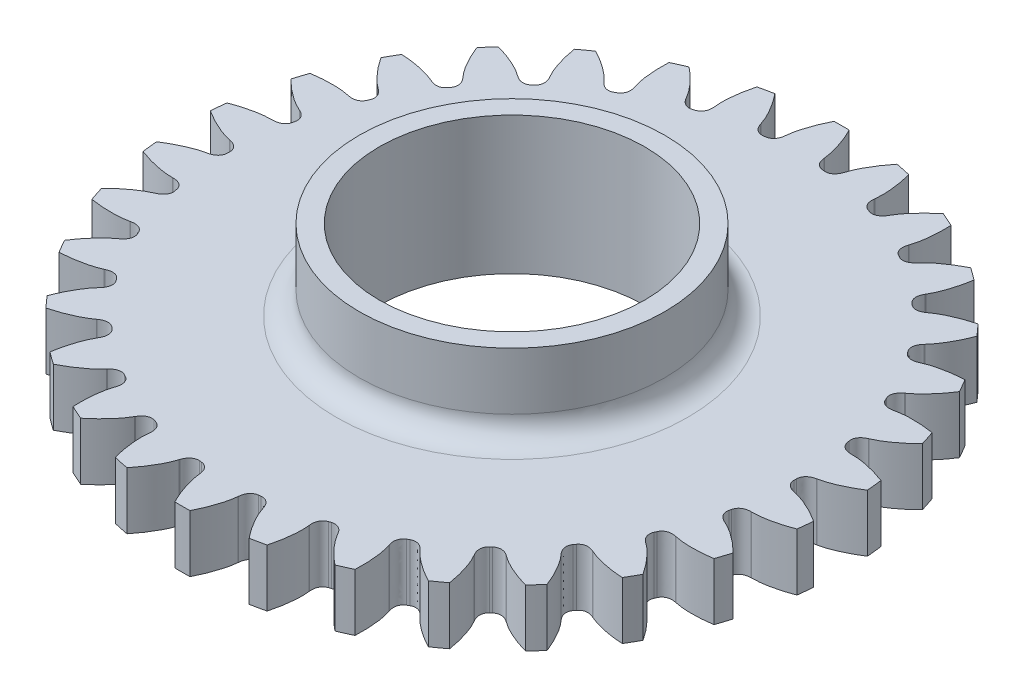
SolidWorks part; units mm, degrees
ref_plane "Front Plane" through (0, 0, 0) normal (0, 0, 1) x (1, 0, 0)
ref_plane "Top Plane" through (0, 0, 0) normal (0, 1, 0) x (1, 0, 0)
ref_plane "Right Plane" through (0, 0, 0) normal (1, 0, 0) x (0, 0, -1)
sketch "Sketch8" plane through (0, 0, 0) normal (0, 1, 0) x (1, 0, 0)
  line L120 (-25.6103, -0.9826) -> (-25.6615, -0.994)
  line L121 (-25.6615, 0.994) -> (-25.6103, 0.9826)
  line L122 (-25.255, 4.3635) -> (-25.3074, 4.363)
  line L123 (-24.894, 6.3076) -> (-24.8464, 6.2858)
  line L124 (-23.7959, 9.519) -> (-23.8472, 9.5294)
  line L125 (-23.0386, 11.3455) -> (-22.9965, 11.3143)
  line L126 (-21.2968, 14.2584) -> (-21.3448, 14.2793)
  line L127 (-20.1763, 15.8876) -> (-20.1416, 15.8483)
  line L128 (-17.8669, 18.3747) -> (-17.9096, 18.4051)
  line L129 (-16.4322, 19.7353) -> (-16.4064, 19.6897)
  line L130 (-13.6562, 21.6879) -> (-13.6916, 21.7265)
  line L131 (-11.9699, 22.7205) -> (-11.9542, 22.6705)
  line L132 (-8.8486, 24.0532) -> (-8.8752, 24.0983)
  line L133 (-6.9845, 24.7127) -> (-6.9795, 24.6605)
  line L134 (-3.6543, 25.3673) -> (-3.6709, 25.417)
  line L135 (-1.6938, 25.6248) -> (-1.6998, 25.5728)
  line L136 (1.6998, 25.5728) -> (1.6938, 25.6248)
  line L137 (3.6709, 25.417) -> (3.6543, 25.3673)
  line L138 (6.9795, 24.6605) -> (6.9845, 24.7127)
  line L139 (8.8752, 24.0983) -> (8.8486, 24.0532)
  line L140 (11.9542, 22.6705) -> (11.9699, 22.7205)
  line L141 (13.6916, 21.7265) -> (13.6562, 21.6879)
  line L142 (16.4064, 19.6897) -> (16.4322, 19.7353)
  line L143 (17.9096, 18.4051) -> (17.8669, 18.3747)
  line L144 (20.1416, 15.8483) -> (20.1763, 15.8876)
  line L145 (21.3448, 14.2793) -> (21.2968, 14.2584)
  line L146 (22.9965, 11.3143) -> (23.0386, 11.3455)
  line L147 (23.8472, 9.5294) -> (23.7959, 9.519)
  line L148 (24.8464, 6.2858) -> (24.894, 6.3076)
  line L149 (25.3074, 4.363) -> (25.255, 4.3635)
  line L150 (25.6103, 0.9826) -> (25.6615, 0.994)
  line L151 (25.6615, -0.994) -> (25.6103, -0.9826)
  line L152 (25.255, -4.3635) -> (25.3074, -4.363)
  line L153 (24.894, -6.3076) -> (24.8464, -6.2858)
  line L154 (23.7959, -9.519) -> (23.8472, -9.5294)
  line L155 (23.0386, -11.3455) -> (22.9965, -11.3143)
  line L156 (21.2968, -14.2584) -> (21.3448, -14.2793)
  line L157 (20.1763, -15.8876) -> (20.1416, -15.8483)
  line L158 (17.8669, -18.3747) -> (17.9096, -18.4051)
  line L159 (16.4322, -19.7353) -> (16.4064, -19.6897)
  line L160 (13.6562, -21.6879) -> (13.6916, -21.7265)
  line L161 (11.9699, -22.7205) -> (11.9542, -22.6705)
  line L162 (8.8486, -24.0532) -> (8.8752, -24.0983)
  line L163 (6.9845, -24.7127) -> (6.9795, -24.6605)
  line L164 (3.6543, -25.3673) -> (3.6709, -25.417)
  line L165 (1.6938, -25.6248) -> (1.6998, -25.5728)
  line L166 (-1.6998, -25.5728) -> (-1.6938, -25.6248)
  line L167 (-3.6709, -25.417) -> (-3.6543, -25.3673)
  line L168 (-6.9795, -24.6605) -> (-6.9845, -24.7127)
  line L169 (-8.8752, -24.0983) -> (-8.8486, -24.0532)
  line L170 (-11.9542, -22.6705) -> (-11.9699, -22.7205)
  line L171 (-13.6916, -21.7265) -> (-13.6562, -21.6879)
  line L172 (-16.4064, -19.6897) -> (-16.4322, -19.7353)
  line L173 (-17.9096, -18.4051) -> (-17.8669, -18.3747)
  line L174 (-20.1416, -15.8483) -> (-20.1763, -15.8876)
  line L175 (-21.3448, -14.2793) -> (-21.2968, -14.2584)
  line L176 (-22.9965, -11.3143) -> (-23.0386, -11.3455)
  line L177 (-23.8472, -9.5294) -> (-23.7959, -9.519)
  line L178 (-24.8464, -6.2858) -> (-24.894, -6.3076)
  line L179 (-25.3074, -4.363) -> (-25.255, -4.3635)
  arc A120 (-28.704, -2.3497) -> (-28.5653, -3.6696) centre (0, 0) ccw
  arc A121 (-24.7498, 0.1062) -> (-24.7498, -0.1062) centre (0, 0) ccw
  arc A122 (-28.5653, 3.6696) -> (-28.704, 2.3497) centre (0, 0) ccw
  arc A123 (-24.1869, 5.2496) -> (-24.231, 5.0419) centre (0, 0) ccw
  arc A124 (-27.1781, 9.5284) -> (-27.5882, 8.2662) centre (0, 0) ccw
  arc A125 (-22.5669, 10.1636) -> (-22.6532, 9.9696) centre (0, 0) ccw
  arc A126 (-24.6031, 14.9709) -> (-25.2667, 13.8215) centre (0, 0) ccw
  arc A127 (-19.9606, 14.6335) -> (-20.0854, 14.4616) centre (0, 0) ccw
  arc A128 (-20.9529, 19.759) -> (-21.8409, 18.7727) centre (0, 0) ccw
  arc A129 (-16.4819, 18.4637) -> (-16.6397, 18.3216) centre (0, 0) ccw
  arc A130 (-16.3869, 23.6836) -> (-17.4606, 22.9034) centre (0, 0) ccw
  arc A131 (-12.2829, 21.487) -> (-12.4668, 21.3808) centre (0, 0) ccw
  arc A132 (-11.1047, 26.573) -> (-12.3171, 26.0332) centre (0, 0) ccw
  arc A133 (-7.5471, 23.5712) -> (-7.7491, 23.5056) centre (0, 0) ccw
  arc A134 (-5.3372, 28.3011) -> (-6.6354, 28.0252) centre (0, 0) ccw
  arc A135 (-2.4814, 24.6253) -> (-2.6927, 24.6031) centre (0, 0) ccw
  arc A136 (0.6636, 28.7924) -> (-0.6636, 28.7924) centre (0, 0) ccw
  arc A137 (2.6927, 24.6031) -> (2.4814, 24.6253) centre (0, 0) ccw
  arc A138 (6.6354, 28.0252) -> (5.3372, 28.3011) centre (0, 0) ccw
  arc A139 (7.7491, 23.5056) -> (7.5471, 23.5712) centre (0, 0) ccw
  arc A140 (12.3171, 26.0332) -> (11.1047, 26.573) centre (0, 0) ccw
  arc A141 (12.4668, 21.3808) -> (12.2829, 21.487) centre (0, 0) ccw
  arc A142 (17.4606, 22.9034) -> (16.3869, 23.6836) centre (0, 0) ccw
  arc A143 (16.6397, 18.3216) -> (16.4819, 18.4637) centre (0, 0) ccw
  arc A144 (21.8409, 18.7727) -> (20.9529, 19.759) centre (0, 0) ccw
  arc A145 (20.0854, 14.4616) -> (19.9606, 14.6335) centre (0, 0) ccw
  arc A146 (25.2667, 13.8215) -> (24.6031, 14.9709) centre (0, 0) ccw
  arc A147 (22.6532, 9.9696) -> (22.5669, 10.1636) centre (0, 0) ccw
  arc A148 (27.5882, 8.2662) -> (27.1781, 9.5284) centre (0, 0) ccw
  arc A149 (24.231, 5.0419) -> (24.1869, 5.2496) centre (0, 0) ccw
  arc A150 (28.704, 2.3497) -> (28.5653, 3.6696) centre (0, 0) ccw
  arc A151 (24.7498, -0.1062) -> (24.7498, 0.1062) centre (0, 0) ccw
  arc A152 (28.5653, -3.6696) -> (28.704, -2.3497) centre (0, 0) ccw
  arc A153 (24.1869, -5.2496) -> (24.231, -5.0419) centre (0, 0) ccw
  arc A154 (27.1781, -9.5284) -> (27.5882, -8.2662) centre (0, 0) ccw
  arc A155 (22.5669, -10.1636) -> (22.6532, -9.9696) centre (0, 0) ccw
  arc A156 (24.6031, -14.9709) -> (25.2667, -13.8215) centre (0, 0) ccw
  arc A157 (19.9606, -14.6335) -> (20.0854, -14.4616) centre (0, 0) ccw
  arc A158 (20.9529, -19.759) -> (21.8409, -18.7727) centre (0, 0) ccw
  arc A159 (16.4819, -18.4637) -> (16.6397, -18.3216) centre (0, 0) ccw
  arc A160 (16.3869, -23.6836) -> (17.4606, -22.9034) centre (0, 0) ccw
  arc A161 (12.2829, -21.487) -> (12.4668, -21.3808) centre (0, 0) ccw
  arc A162 (11.1047, -26.573) -> (12.3171, -26.0332) centre (0, 0) ccw
  arc A163 (7.5471, -23.5712) -> (7.7491, -23.5056) centre (0, 0) ccw
  arc A164 (5.3372, -28.3011) -> (6.6354, -28.0252) centre (0, 0) ccw
  arc A165 (2.4814, -24.6253) -> (2.6927, -24.6031) centre (0, 0) ccw
  arc A166 (-0.6636, -28.7924) -> (0.6636, -28.7924) centre (0, 0) ccw
  arc A167 (-2.6927, -24.6031) -> (-2.4814, -24.6253) centre (0, 0) ccw
  arc A168 (-6.6354, -28.0252) -> (-5.3372, -28.3011) centre (0, 0) ccw
  arc A169 (-7.7491, -23.5056) -> (-7.5471, -23.5712) centre (0, 0) ccw
  arc A170 (-12.3171, -26.0332) -> (-11.1047, -26.573) centre (0, 0) ccw
  arc A171 (-12.4668, -21.3808) -> (-12.2829, -21.487) centre (0, 0) ccw
  arc A172 (-17.4606, -22.9034) -> (-16.3869, -23.6836) centre (0, 0) ccw
  arc A173 (-16.6397, -18.3216) -> (-16.4819, -18.4637) centre (0, 0) ccw
  arc A174 (-21.8409, -18.7727) -> (-20.9529, -19.759) centre (0, 0) ccw
  arc A175 (-20.0854, -14.4616) -> (-19.9606, -14.6335) centre (0, 0) ccw
  arc A176 (-25.2667, -13.8215) -> (-24.6031, -14.9709) centre (0, 0) ccw
  arc A177 (-22.6532, -9.9696) -> (-22.5669, -10.1636) centre (0, 0) ccw
  arc A178 (-27.5882, -8.2662) -> (-27.1781, -9.5284) centre (0, 0) ccw
  arc A179 (-24.231, -5.0419) -> (-24.1869, -5.2496) centre (0, 0) ccw
  spline S240 degree 3 poles (-25.6615, -0.994) (-25.8209, -1.0255) (-26.0845, -1.093) (-26.4652, -1.2166) (-26.8252, -1.3524) (-27.2303, -1.5274) (-27.6774, -1.7459) (-28.1632, -2.0124) (-28.5074, -2.2228) (-28.6912, -2.3414) (-28.704, -2.3497) knots 0 0 0 0 0.103847 0.173799 0.255771 0.349761 0.455771 0.573799 0.703847 0.713589 0.713589 0.713589 0.713589
  spline S241 degree 3 poles (-24.7498, -0.1062) (-24.7485, -0.2459) (-24.8034, -0.4407) (-24.9485, -0.6376) (-25.0551, -0.7378) (-25.1596, -0.8112) (-25.2608, -0.8666) (-25.3601, -0.9098) (-25.4756, -0.9499) (-25.5594, -0.9724) (-25.6103, -0.9826) knots 0 0 0 0 0.312247 0.438755 0.546198 0.639977 0.72507 0.805244 0.883176 1 1 1 1
  spline S242 degree 3 poles (-25.6103, 0.9826) (-25.5594, 0.9724) (-25.4756, 0.9499) (-25.3601, 0.9098) (-25.2608, 0.8666) (-25.1596, 0.8112) (-25.0551, 0.7378) (-24.9485, 0.6376) (-24.8034, 0.4407) (-24.7485, 0.2459) (-24.7498, 0.1062) knots 0 0 0 0 0.116824 0.194756 0.27493 0.360023 0.453802 0.561245 0.687753 1 1 1 1
  spline S243 degree 3 poles (-28.704, 2.3497) (-28.6912, 2.3414) (-28.5074, 2.2228) (-28.1632, 2.0124) (-27.6774, 1.7459) (-27.2303, 1.5274) (-26.8252, 1.3524) (-26.4652, 1.2166) (-26.0845, 1.093) (-25.8209, 1.0255) (-25.6615, 0.994) knots 0.286411 0.286411 0.286411 0.286411 0.296153 0.426201 0.544229 0.650239 0.744229 0.826201 0.896153 1 1 1 1
  spline S244 degree 3 poles (-25.3074, 4.363) (-25.4698, 4.3653) (-25.7417, 4.3541) (-26.1398, 4.3124) (-26.5202, 4.2544) (-26.9528, 4.1675) (-27.4356, 4.0467) (-27.9662, 3.887) (-28.3466, 3.7528) (-28.551, 3.675) (-28.5653, 3.6696) knots 0 0 0 0 0.103847 0.173799 0.255771 0.349761 0.455771 0.573799 0.703847 0.713589 0.713589 0.713589 0.713589
  spline S245 degree 3 poles (-24.231, 5.0419) (-24.2588, 4.905) (-24.3531, 4.7259) (-24.5359, 4.5635) (-24.661, 4.4876) (-24.7784, 4.4375) (-24.889, 4.4044) (-24.9951, 4.3828) (-25.1164, 4.3675) (-25.203, 4.363) (-25.255, 4.3635) knots 0 0 0 0 0.312247 0.438755 0.546198 0.639977 0.72507 0.805244 0.883176 1 1 1 1
  spline S246 degree 3 poles (-24.8464, 6.2858) (-24.7987, 6.2652) (-24.7214, 6.2258) (-24.6168, 6.1626) (-24.5286, 6.0997) (-24.4411, 6.0245) (-24.3542, 5.931) (-24.2708, 5.8107) (-24.1698, 5.588) (-24.1566, 5.386) (-24.1869, 5.2496) knots 0 0 0 0 0.116824 0.194756 0.27493 0.360023 0.453802 0.561245 0.687753 1 1 1 1
  spline S247 degree 3 poles (-27.5882, 8.2662) (-27.5774, 8.2554) (-27.4223, 8.1013) (-27.1294, 7.8239) (-26.7096, 7.4622) (-26.3177, 7.1555) (-25.9578, 6.9002) (-25.6339, 6.6924) (-25.2872, 6.4924) (-25.0434, 6.3716) (-24.894, 6.3076) knots 0.286411 0.286411 0.286411 0.286411 0.296153 0.426201 0.544229 0.650239 0.744229 0.826201 0.896153 1 1 1 1
  spline S248 degree 3 poles (-23.8472, 9.5294) (-24.0057, 9.5654) (-24.274, 9.611) (-24.672, 9.6529) (-25.0561, 9.6753) (-25.4974, 9.6802) (-25.9947, 9.6624) (-26.5469, 9.6166) (-26.9469, 9.5644) (-27.163, 9.5308) (-27.1781, 9.5284) knots 0 0 0 0 0.103847 0.173799 0.255771 0.349761 0.455771 0.573799 0.703847 0.713589 0.713589 0.713589 0.713589
  spline S249 degree 3 poles (-22.6532, 9.9696) (-22.7089, 9.8415) (-22.8383, 9.6859) (-23.0509, 9.565) (-23.1891, 9.5168) (-23.3144, 9.4922) (-23.4294, 9.4828) (-23.5376, 9.4838) (-23.6595, 9.4941) (-23.7452, 9.5076) (-23.7959, 9.519) knots 0 0 0 0 0.312247 0.438755 0.546198 0.639977 0.72507 0.805244 0.883176 1 1 1 1
  spline S250 degree 3 poles (-22.9965, 11.3143) (-22.9542, 11.2843) (-22.8868, 11.2297) (-22.7976, 11.146) (-22.7244, 11.0662) (-22.6545, 10.9744) (-22.5889, 10.8649) (-22.5323, 10.7299) (-22.4798, 10.4911) (-22.5089, 10.2907) (-22.5669, 10.1636) knots 0 0 0 0 0.116824 0.194756 0.27493 0.360023 0.453802 0.561245 0.687753 1 1 1 1
  spline S251 degree 3 poles (-25.2667, 13.8215) (-25.2584, 13.8087) (-25.1387, 13.6257) (-24.9099, 13.2934) (-24.5744, 12.8524) (-24.2549, 12.4709) (-23.956, 12.1463) (-23.6823, 11.8758) (-23.3848, 11.6081) (-23.1714, 11.4392) (-23.0386, 11.3455) knots 0.286411 0.286411 0.286411 0.286411 0.296153 0.426201 0.544229 0.650239 0.744229 0.826201 0.896153 1 1 1 1
  spline S252 degree 3 poles (-21.3448, 14.2793) (-21.4923, 14.3475) (-21.7453, 14.4478) (-22.1259, 14.5716) (-22.497, 14.6733) (-22.9275, 14.7699) (-23.4177, 14.8559) (-23.9674, 14.9259) (-24.3695, 14.9579) (-24.5879, 14.9701) (-24.6031, 14.9709) knots 0 0 0 0 0.103847 0.173799 0.255771 0.349761 0.455771 0.573799 0.703847 0.713589 0.713589 0.713589 0.713589
  spline S253 degree 3 poles (-20.0854, 14.4616) (-20.1665, 14.3479) (-20.3254, 14.2226) (-20.5585, 14.1486) (-20.7037, 14.1301) (-20.8314, 14.1321) (-20.9458, 14.1469) (-21.0515, 14.1703) (-21.1686, 14.2057) (-21.2495, 14.2368) (-21.2968, 14.2584) knots 0 0 0 0 0.312247 0.438755 0.546198 0.639977 0.72507 0.805244 0.883176 1 1 1 1
  spline S254 degree 3 poles (-20.1416, 15.8483) (-20.1064, 15.8101) (-20.0519, 15.7427) (-19.982, 15.6423) (-19.9271, 15.549) (-19.8777, 15.4447) (-19.8364, 15.324) (-19.809, 15.1802) (-19.8074, 14.9356) (-19.8775, 14.7457) (-19.9606, 14.6335) knots 0 0 0 0 0.116824 0.194756 0.27493 0.360023 0.453802 0.561245 0.687753 1 1 1 1
  spline S255 degree 3 poles (-21.8409, 18.7727) (-21.8354, 18.7585) (-21.7564, 18.5546) (-21.6017, 18.182) (-21.3653, 17.6809) (-21.132, 17.2412) (-20.9071, 16.8616) (-20.6957, 16.5401) (-20.4603, 16.2164) (-20.2867, 16.0068) (-20.1763, 15.8876) knots 0.286411 0.286411 0.286411 0.286411 0.296153 0.426201 0.544229 0.650239 0.744229 0.826201 0.896153 1 1 1 1
  spline S256 degree 3 poles (-17.9096, 18.4051) (-18.0396, 18.5024) (-18.2662, 18.6532) (-18.6128, 18.8534) (-18.9546, 19.0301) (-19.3557, 19.214) (-19.8173, 19.4001) (-20.3404, 19.5828) (-20.7271, 19.6978) (-20.9381, 19.755) (-20.9529, 19.759) knots 0 0 0 0 0.103847 0.173799 0.255771 0.349761 0.455771 0.573799 0.703847 0.713589 0.713589 0.713589 0.713589
  spline S257 degree 3 poles (-16.6397, 18.3216) (-16.7427, 18.2272) (-16.9243, 18.1377) (-17.1676, 18.1138) (-17.3135, 18.1259) (-17.4379, 18.1544) (-17.5468, 18.1926) (-17.6453, 18.2375) (-17.7525, 18.2965) (-17.8252, 18.3437) (-17.8669, 18.3747) knots 0 0 0 0 0.312247 0.438755 0.546198 0.639977 0.72507 0.805244 0.883176 1 1 1 1
  spline S258 degree 3 poles (-16.4064, 19.6897) (-16.3799, 19.645) (-16.3406, 19.5677) (-16.2931, 19.455) (-16.2588, 19.3523) (-16.2322, 19.24) (-16.2169, 19.1133) (-16.22, 18.967) (-16.2692, 18.7274) (-16.3773, 18.5563) (-16.4819, 18.4637) knots 0 0 0 0 0.116824 0.194756 0.27493 0.360023 0.453802 0.561245 0.687753 1 1 1 1
  spline S259 degree 3 poles (-17.4606, 22.9034) (-17.4582, 22.8884) (-17.4233, 22.6725) (-17.3494, 22.2759) (-17.2223, 21.7366) (-17.0856, 21.2581) (-16.9445, 20.84) (-16.8046, 20.4815) (-16.6416, 20.1159) (-16.5154, 19.8749) (-16.4322, 19.7353) knots 0.286411 0.286411 0.286411 0.286411 0.296153 0.426201 0.544229 0.650239 0.744229 0.826201 0.896153 1 1 1 1
  spline S260 degree 3 poles (-13.6916, 21.7265) (-13.7986, 21.8488) (-13.9888, 22.0433) (-14.2862, 22.3112) (-14.5838, 22.5551) (-14.9379, 22.8184) (-15.3507, 23.0964) (-15.8244, 23.3839) (-16.1787, 23.5767) (-16.3733, 23.6766) (-16.3869, 23.6836) knots 0 0 0 0 0.103847 0.173799 0.255771 0.349761 0.455771 0.573799 0.703847 0.713589 0.713589 0.713589 0.713589
  spline S261 degree 3 poles (-12.4668, 21.3808) (-12.5872, 21.3099) (-12.7834, 21.2601) (-13.0264, 21.2873) (-13.1665, 21.3295) (-13.2823, 21.3832) (-13.3809, 21.4432) (-13.4679, 21.5076) (-13.5605, 21.5876) (-13.6218, 21.6489) (-13.6562, 21.6879) knots 0 0 0 0 0.312247 0.438755 0.546198 0.639977 0.72507 0.805244 0.883176 1 1 1 1
  spline S262 degree 3 poles (-11.9542, 22.6705) (-11.9376, 22.6213) (-11.9152, 22.5375) (-11.8922, 22.4174) (-11.8799, 22.3098) (-11.8773, 22.1944) (-11.8886, 22.0673) (-11.9221, 21.9249) (-12.0201, 21.7008) (-12.1613, 21.5558) (-12.2829, 21.487) knots 0 0 0 0 0.116824 0.194756 0.27493 0.360023 0.453802 0.561245 0.687753 1 1 1 1
  spline S263 degree 3 poles (-12.3171, 26.0332) (-12.3179, 26.018) (-12.3287, 25.7996) (-12.3388, 25.3963) (-12.3267, 24.8423) (-12.2924, 24.3458) (-12.2414, 23.9075) (-12.179, 23.5278) (-12.0956, 23.1364) (-12.0223, 22.8743) (-11.9699, 22.7205) knots 0.286411 0.286411 0.286411 0.286411 0.296153 0.426201 0.544229 0.650239 0.744229 0.826201 0.896153 1 1 1 1
  spline S264 degree 3 poles (-8.8752, 24.0983) (-8.9544, 24.2402) (-9.1001, 24.4701) (-9.3352, 24.7939) (-9.5757, 25.0944) (-9.8672, 25.4256) (-10.2133, 25.7833) (-10.6168, 26.1629) (-10.9233, 26.4253) (-11.0928, 26.5634) (-11.1047, 26.573) knots 0 0 0 0 0.103847 0.173799 0.255771 0.349761 0.455771 0.573799 0.703847 0.713589 0.713589 0.713589 0.713589
  spline S265 degree 3 poles (-7.7491, 23.5056) (-7.8815, 23.4613) (-8.0838, 23.4533) (-8.3159, 23.5304) (-8.4442, 23.6009) (-8.5463, 23.6775) (-8.6302, 23.7567) (-8.7019, 23.8377) (-8.7758, 23.9352) (-8.8231, 24.0079) (-8.8486, 24.0532) knots 0 0 0 0 0.312247 0.438755 0.546198 0.639977 0.72507 0.805244 0.883176 1 1 1 1
  spline S266 degree 3 poles (-6.9795, 24.6605) (-6.9735, 24.6089) (-6.969, 24.5223) (-6.9715, 24.4) (-6.9819, 24.2922) (-7.0032, 24.1789) (-7.0408, 24.0569) (-7.1032, 23.9245) (-7.2456, 23.7257) (-7.4139, 23.6132) (-7.5471, 23.5712) knots 0 0 0 0 0.116824 0.194756 0.27493 0.360023 0.453802 0.561245 0.687753 1 1 1 1
  spline S267 degree 3 poles (-6.6354, 28.0252) (-6.6393, 28.0105) (-6.6952, 27.7991) (-6.789, 27.4067) (-6.8923, 26.8623) (-6.962, 26.3695) (-7.0032, 25.9302) (-7.0211, 25.5458) (-7.021, 25.1456) (-7.0038, 24.874) (-6.9845, 24.7127) knots 0.286411 0.286411 0.286411 0.286411 0.296153 0.426201 0.544229 0.650239 0.744229 0.826201 0.896153 1 1 1 1
  spline S268 degree 3 poles (-3.6709, 25.417) (-3.7189, 25.5722) (-3.8136, 25.8273) (-3.9763, 26.193) (-4.149, 26.5369) (-4.3653, 26.9215) (-4.6294, 27.3433) (-4.9452, 27.7986) (-5.1905, 28.1189) (-5.3276, 28.2893) (-5.3372, 28.3011) knots 0 0 0 0 0.103847 0.173799 0.255771 0.349761 0.455771 0.573799 0.703847 0.713589 0.713589 0.713589 0.713589
  spline S269 degree 3 poles (-2.6927, 24.6031) (-2.8314, 24.5873) (-3.031, 24.6215) (-3.2419, 24.7452) (-3.3528, 24.8408) (-3.4367, 24.937) (-3.5023, 25.0318) (-3.5556, 25.1261) (-3.6076, 25.2368) (-3.6388, 25.3177) (-3.6543, 25.3673) knots 0 0 0 0 0.312247 0.438755 0.546198 0.639977 0.72507 0.805244 0.883176 1 1 1 1
  spline S270 degree 3 poles (-1.6998, 25.5728) (-1.7046, 25.521) (-1.7182, 25.4354) (-1.7461, 25.3163) (-1.7786, 25.213) (-1.8231, 25.1065) (-1.8852, 24.995) (-1.9738, 24.8785) (-2.1544, 24.7136) (-2.3424, 24.6387) (-2.4814, 24.6253) knots 0 0 0 0 0.116824 0.194756 0.27493 0.360023 0.453802 0.561245 0.687753 1 1 1 1
  spline S271 degree 3 poles (-0.6636, 28.7924) (-0.6705, 28.7788) (-0.7692, 28.5836) (-0.9425, 28.2193) (-1.1567, 27.7083) (-1.3273, 27.2408) (-1.459, 26.8196) (-1.5564, 26.4474) (-1.6395, 26.0559) (-1.6791, 25.7866) (-1.6938, 25.6248) knots 0.286411 0.286411 0.286411 0.286411 0.296153 0.426201 0.544229 0.650239 0.744229 0.826201 0.896153 1 1 1 1
  spline S272 degree 3 poles (1.6938, 25.6248) (1.6791, 25.7866) (1.6395, 26.0559) (1.5564, 26.4474) (1.459, 26.8196) (1.3273, 27.2408) (1.1567, 27.7083) (0.9425, 28.2193) (0.7692, 28.5836) (0.6705, 28.7788) (0.6636, 28.7924) knots 0 0 0 0 0.103847 0.173799 0.255771 0.349761 0.455771 0.573799 0.703847 0.713589 0.713589 0.713589 0.713589
  spline S273 degree 3 poles (2.4814, 24.6253) (2.3424, 24.6387) (2.1544, 24.7136) (1.9738, 24.8785) (1.8852, 24.995) (1.8231, 25.1065) (1.7786, 25.213) (1.7461, 25.3163) (1.7182, 25.4354) (1.7046, 25.521) (1.6998, 25.5728) knots 0 0 0 0 0.312247 0.438755 0.546198 0.639977 0.72507 0.805244 0.883176 1 1 1 1
  spline S274 degree 3 poles (3.6543, 25.3673) (3.6388, 25.3177) (3.6076, 25.2368) (3.5556, 25.1261) (3.5023, 25.0318) (3.4367, 24.937) (3.3528, 24.8408) (3.2419, 24.7452) (3.031, 24.6215) (2.8314, 24.5873) (2.6927, 24.6031) knots 0 0 0 0 0.116824 0.194756 0.27493 0.360023 0.453802 0.561245 0.687753 1 1 1 1
  spline S275 degree 3 poles (5.3372, 28.3011) (5.3276, 28.2893) (5.1905, 28.1189) (4.9452, 27.7986) (4.6294, 27.3433) (4.3653, 26.9215) (4.149, 26.5369) (3.9763, 26.193) (3.8136, 25.8273) (3.7189, 25.5722) (3.6709, 25.417) knots 0.286411 0.286411 0.286411 0.286411 0.296153 0.426201 0.544229 0.650239 0.744229 0.826201 0.896153 1 1 1 1
  spline S276 degree 3 poles (6.9845, 24.7127) (7.0038, 24.874) (7.021, 25.1456) (7.0211, 25.5458) (7.0032, 25.9302) (6.962, 26.3695) (6.8923, 26.8623) (6.789, 27.4067) (6.6952, 27.7991) (6.6393, 28.0105) (6.6354, 28.0252) knots 0 0 0 0 0.103847 0.173799 0.255771 0.349761 0.455771 0.573799 0.703847 0.713589 0.713589 0.713589 0.713589
  spline S277 degree 3 poles (7.5471, 23.5712) (7.4139, 23.6132) (7.2456, 23.7257) (7.1032, 23.9245) (7.0408, 24.0569) (7.0032, 24.1789) (6.9819, 24.2922) (6.9715, 24.4) (6.969, 24.5223) (6.9735, 24.6089) (6.9795, 24.6605) knots 0 0 0 0 0.312247 0.438755 0.546198 0.639977 0.72507 0.805244 0.883176 1 1 1 1
  spline S278 degree 3 poles (8.8486, 24.0532) (8.8231, 24.0079) (8.7758, 23.9352) (8.7019, 23.8377) (8.6302, 23.7567) (8.5463, 23.6775) (8.4442, 23.6009) (8.3159, 23.5304) (8.0838, 23.4533) (7.8815, 23.4613) (7.7491, 23.5056) knots 0 0 0 0 0.116824 0.194756 0.27493 0.360023 0.453802 0.561245 0.687753 1 1 1 1
  spline S279 degree 3 poles (11.1047, 26.573) (11.0928, 26.5634) (10.9233, 26.4253) (10.6168, 26.1629) (10.2133, 25.7833) (9.8672, 25.4256) (9.5757, 25.0944) (9.3352, 24.7939) (9.1001, 24.4701) (8.9544, 24.2402) (8.8752, 24.0983) knots 0.286411 0.286411 0.286411 0.286411 0.296153 0.426201 0.544229 0.650239 0.744229 0.826201 0.896153 1 1 1 1
  spline S280 degree 3 poles (11.9699, 22.7205) (12.0223, 22.8743) (12.0956, 23.1364) (12.179, 23.5278) (12.2414, 23.9075) (12.2924, 24.3458) (12.3267, 24.8423) (12.3388, 25.3963) (12.3287, 25.7996) (12.3179, 26.018) (12.3171, 26.0332) knots 0 0 0 0 0.103847 0.173799 0.255771 0.349761 0.455771 0.573799 0.703847 0.713589 0.713589 0.713589 0.713589
  spline S281 degree 3 poles (12.2829, 21.487) (12.1613, 21.5558) (12.0201, 21.7008) (11.9221, 21.9249) (11.8886, 22.0673) (11.8773, 22.1944) (11.8799, 22.3098) (11.8922, 22.4174) (11.9152, 22.5375) (11.9376, 22.6213) (11.9542, 22.6705) knots 0 0 0 0 0.312247 0.438755 0.546198 0.639977 0.72507 0.805244 0.883176 1 1 1 1
  spline S282 degree 3 poles (13.6562, 21.6879) (13.6218, 21.6489) (13.5605, 21.5876) (13.4679, 21.5076) (13.3809, 21.4432) (13.2823, 21.3832) (13.1665, 21.3295) (13.0264, 21.2873) (12.7834, 21.2601) (12.5872, 21.3099) (12.4668, 21.3808) knots 0 0 0 0 0.116824 0.194756 0.27493 0.360023 0.453802 0.561245 0.687753 1 1 1 1
  spline S283 degree 3 poles (16.3869, 23.6836) (16.3733, 23.6766) (16.1787, 23.5767) (15.8244, 23.3839) (15.3507, 23.0964) (14.9379, 22.8184) (14.5838, 22.5551) (14.2862, 22.3112) (13.9888, 22.0433) (13.7986, 21.8488) (13.6916, 21.7265) knots 0.286411 0.286411 0.286411 0.286411 0.296153 0.426201 0.544229 0.650239 0.744229 0.826201 0.896153 1 1 1 1
  spline S284 degree 3 poles (16.4322, 19.7353) (16.5154, 19.8749) (16.6416, 20.1159) (16.8046, 20.4815) (16.9445, 20.84) (17.0856, 21.2581) (17.2223, 21.7366) (17.3494, 22.2759) (17.4233, 22.6725) (17.4582, 22.8884) (17.4606, 22.9034) knots 0 0 0 0 0.103847 0.173799 0.255771 0.349761 0.455771 0.573799 0.703847 0.713589 0.713589 0.713589 0.713589
  spline S285 degree 3 poles (16.4819, 18.4637) (16.3773, 18.5563) (16.2692, 18.7274) (16.22, 18.967) (16.2169, 19.1133) (16.2322, 19.24) (16.2588, 19.3523) (16.2931, 19.455) (16.3406, 19.5677) (16.3799, 19.645) (16.4064, 19.6897) knots 0 0 0 0 0.312247 0.438755 0.546198 0.639977 0.72507 0.805244 0.883176 1 1 1 1
  spline S286 degree 3 poles (17.8669, 18.3747) (17.8252, 18.3437) (17.7525, 18.2965) (17.6453, 18.2375) (17.5468, 18.1926) (17.4379, 18.1544) (17.3135, 18.1259) (17.1676, 18.1138) (16.9243, 18.1377) (16.7427, 18.2272) (16.6397, 18.3216) knots 0 0 0 0 0.116824 0.194756 0.27493 0.360023 0.453802 0.561245 0.687753 1 1 1 1
  spline S287 degree 3 poles (20.9529, 19.759) (20.9381, 19.755) (20.7271, 19.6978) (20.3404, 19.5828) (19.8173, 19.4001) (19.3557, 19.214) (18.9546, 19.0301) (18.6128, 18.8534) (18.2662, 18.6532) (18.0396, 18.5024) (17.9096, 18.4051) knots 0.286411 0.286411 0.286411 0.286411 0.296153 0.426201 0.544229 0.650239 0.744229 0.826201 0.896153 1 1 1 1
  spline S288 degree 3 poles (20.1763, 15.8876) (20.2867, 16.0068) (20.4603, 16.2164) (20.6957, 16.5401) (20.9071, 16.8616) (21.132, 17.2412) (21.3653, 17.6809) (21.6017, 18.182) (21.7564, 18.5546) (21.8354, 18.7585) (21.8409, 18.7727) knots 0 0 0 0 0.103847 0.173799 0.255771 0.349761 0.455771 0.573799 0.703847 0.713589 0.713589 0.713589 0.713589
  spline S289 degree 3 poles (19.9606, 14.6335) (19.8775, 14.7457) (19.8074, 14.9356) (19.809, 15.1802) (19.8364, 15.324) (19.8777, 15.4447) (19.9271, 15.549) (19.982, 15.6423) (20.0519, 15.7427) (20.1064, 15.8101) (20.1416, 15.8483) knots 0 0 0 0 0.312247 0.438755 0.546198 0.639977 0.72507 0.805244 0.883176 1 1 1 1
  spline S290 degree 3 poles (21.2968, 14.2584) (21.2495, 14.2368) (21.1686, 14.2057) (21.0515, 14.1703) (20.9458, 14.1469) (20.8314, 14.1321) (20.7037, 14.1301) (20.5585, 14.1486) (20.3254, 14.2226) (20.1665, 14.3479) (20.0854, 14.4616) knots 0 0 0 0 0.116824 0.194756 0.27493 0.360023 0.453802 0.561245 0.687753 1 1 1 1
  spline S291 degree 3 poles (24.6031, 14.9709) (24.5879, 14.9701) (24.3695, 14.9579) (23.9674, 14.9259) (23.4177, 14.8559) (22.9275, 14.7699) (22.497, 14.6733) (22.1259, 14.5716) (21.7453, 14.4478) (21.4923, 14.3475) (21.3448, 14.2793) knots 0.286411 0.286411 0.286411 0.286411 0.296153 0.426201 0.544229 0.650239 0.744229 0.826201 0.896153 1 1 1 1
  spline S292 degree 3 poles (23.0386, 11.3455) (23.1714, 11.4392) (23.3848, 11.6081) (23.6823, 11.8758) (23.956, 12.1463) (24.2549, 12.4709) (24.5744, 12.8524) (24.9099, 13.2934) (25.1387, 13.6257) (25.2584, 13.8087) (25.2667, 13.8215) knots 0 0 0 0 0.103847 0.173799 0.255771 0.349761 0.455771 0.573799 0.703847 0.713589 0.713589 0.713589 0.713589
  spline S293 degree 3 poles (22.5669, 10.1636) (22.5089, 10.2907) (22.4798, 10.4911) (22.5323, 10.7299) (22.5889, 10.8649) (22.6545, 10.9744) (22.7244, 11.0662) (22.7976, 11.146) (22.8868, 11.2297) (22.9542, 11.2843) (22.9965, 11.3143) knots 0 0 0 0 0.312247 0.438755 0.546198 0.639977 0.72507 0.805244 0.883176 1 1 1 1
  spline S294 degree 3 poles (23.7959, 9.519) (23.7452, 9.5076) (23.6595, 9.4941) (23.5376, 9.4838) (23.4294, 9.4828) (23.3144, 9.4922) (23.1891, 9.5168) (23.0509, 9.565) (22.8383, 9.6859) (22.7089, 9.8415) (22.6532, 9.9696) knots 0 0 0 0 0.116824 0.194756 0.27493 0.360023 0.453802 0.561245 0.687753 1 1 1 1
  spline S295 degree 3 poles (27.1781, 9.5284) (27.163, 9.5308) (26.9469, 9.5644) (26.5469, 9.6166) (25.9947, 9.6624) (25.4974, 9.6802) (25.0561, 9.6753) (24.672, 9.6529) (24.274, 9.611) (24.0057, 9.5654) (23.8472, 9.5294) knots 0.286411 0.286411 0.286411 0.286411 0.296153 0.426201 0.544229 0.650239 0.744229 0.826201 0.896153 1 1 1 1
  spline S296 degree 3 poles (24.894, 6.3076) (25.0434, 6.3716) (25.2872, 6.4924) (25.6339, 6.6924) (25.9578, 6.9002) (26.3177, 7.1555) (26.7096, 7.4622) (27.1294, 7.8239) (27.4223, 8.1013) (27.5774, 8.2554) (27.5882, 8.2662) knots 0 0 0 0 0.103847 0.173799 0.255771 0.349761 0.455771 0.573799 0.703847 0.713589 0.713589 0.713589 0.713589
  spline S297 degree 3 poles (24.1869, 5.2496) (24.1566, 5.386) (24.1698, 5.588) (24.2708, 5.8107) (24.3542, 5.931) (24.4411, 6.0245) (24.5286, 6.0997) (24.6168, 6.1626) (24.7214, 6.2258) (24.7987, 6.2652) (24.8464, 6.2858) knots 0 0 0 0 0.312247 0.438755 0.546198 0.639977 0.72507 0.805244 0.883176 1 1 1 1
  spline S298 degree 3 poles (25.255, 4.3635) (25.203, 4.363) (25.1164, 4.3675) (24.9951, 4.3828) (24.889, 4.4044) (24.7784, 4.4375) (24.661, 4.4876) (24.5359, 4.5635) (24.3531, 4.7259) (24.2588, 4.905) (24.231, 5.0419) knots 0 0 0 0 0.116824 0.194756 0.27493 0.360023 0.453802 0.561245 0.687753 1 1 1 1
  spline S299 degree 3 poles (28.5653, 3.6696) (28.551, 3.675) (28.3466, 3.7528) (27.9662, 3.887) (27.4356, 4.0467) (26.9528, 4.1675) (26.5202, 4.2544) (26.1398, 4.3124) (25.7417, 4.3541) (25.4698, 4.3653) (25.3074, 4.363) knots 0.286411 0.286411 0.286411 0.286411 0.296153 0.426201 0.544229 0.650239 0.744229 0.826201 0.896153 1 1 1 1
  spline S300 degree 3 poles (25.6615, 0.994) (25.8209, 1.0255) (26.0845, 1.093) (26.4652, 1.2166) (26.8252, 1.3524) (27.2303, 1.5274) (27.6774, 1.7459) (28.1632, 2.0124) (28.5074, 2.2228) (28.6912, 2.3414) (28.704, 2.3497) knots 0 0 0 0 0.103847 0.173799 0.255771 0.349761 0.455771 0.573799 0.703847 0.713589 0.713589 0.713589 0.713589
  spline S301 degree 3 poles (24.7498, 0.1062) (24.7485, 0.2459) (24.8034, 0.4407) (24.9485, 0.6376) (25.0551, 0.7378) (25.1596, 0.8112) (25.2608, 0.8666) (25.3601, 0.9098) (25.4756, 0.9499) (25.5594, 0.9724) (25.6103, 0.9826) knots 0 0 0 0 0.312247 0.438755 0.546198 0.639977 0.72507 0.805244 0.883176 1 1 1 1
  spline S302 degree 3 poles (25.6103, -0.9826) (25.5594, -0.9724) (25.4756, -0.9499) (25.3601, -0.9098) (25.2608, -0.8666) (25.1596, -0.8112) (25.0551, -0.7378) (24.9485, -0.6376) (24.8034, -0.4407) (24.7485, -0.2459) (24.7498, -0.1062) knots 0 0 0 0 0.116824 0.194756 0.27493 0.360023 0.453802 0.561245 0.687753 1 1 1 1
  spline S303 degree 3 poles (28.704, -2.3497) (28.6912, -2.3414) (28.5074, -2.2228) (28.1632, -2.0124) (27.6774, -1.7459) (27.2303, -1.5274) (26.8252, -1.3524) (26.4652, -1.2166) (26.0845, -1.093) (25.8209, -1.0255) (25.6615, -0.994) knots 0.286411 0.286411 0.286411 0.286411 0.296153 0.426201 0.544229 0.650239 0.744229 0.826201 0.896153 1 1 1 1
  spline S304 degree 3 poles (25.3074, -4.363) (25.4698, -4.3653) (25.7417, -4.3541) (26.1398, -4.3124) (26.5202, -4.2544) (26.9528, -4.1675) (27.4356, -4.0467) (27.9662, -3.887) (28.3466, -3.7528) (28.551, -3.675) (28.5653, -3.6696) knots 0 0 0 0 0.103847 0.173799 0.255771 0.349761 0.455771 0.573799 0.703847 0.713589 0.713589 0.713589 0.713589
  spline S305 degree 3 poles (24.231, -5.0419) (24.2588, -4.905) (24.3531, -4.7259) (24.5359, -4.5635) (24.661, -4.4876) (24.7784, -4.4375) (24.889, -4.4044) (24.9951, -4.3828) (25.1164, -4.3675) (25.203, -4.363) (25.255, -4.3635) knots 0 0 0 0 0.312247 0.438755 0.546198 0.639977 0.72507 0.805244 0.883176 1 1 1 1
  spline S306 degree 3 poles (24.8464, -6.2858) (24.7987, -6.2652) (24.7214, -6.2258) (24.6168, -6.1626) (24.5286, -6.0997) (24.4411, -6.0245) (24.3542, -5.931) (24.2708, -5.8107) (24.1698, -5.588) (24.1566, -5.386) (24.1869, -5.2496) knots 0 0 0 0 0.116824 0.194756 0.27493 0.360023 0.453802 0.561245 0.687753 1 1 1 1
  spline S307 degree 3 poles (27.5882, -8.2662) (27.5774, -8.2554) (27.4223, -8.1013) (27.1294, -7.8239) (26.7096, -7.4622) (26.3177, -7.1555) (25.9578, -6.9002) (25.6339, -6.6924) (25.2872, -6.4924) (25.0434, -6.3716) (24.894, -6.3076) knots 0.286411 0.286411 0.286411 0.286411 0.296153 0.426201 0.544229 0.650239 0.744229 0.826201 0.896153 1 1 1 1
  spline S308 degree 3 poles (23.8472, -9.5294) (24.0057, -9.5654) (24.274, -9.611) (24.672, -9.6529) (25.0561, -9.6753) (25.4974, -9.6802) (25.9947, -9.6624) (26.5469, -9.6166) (26.9469, -9.5644) (27.163, -9.5308) (27.1781, -9.5284) knots 0 0 0 0 0.103847 0.173799 0.255771 0.349761 0.455771 0.573799 0.703847 0.713589 0.713589 0.713589 0.713589
  spline S309 degree 3 poles (22.6532, -9.9696) (22.7089, -9.8415) (22.8383, -9.6859) (23.0509, -9.565) (23.1891, -9.5168) (23.3144, -9.4922) (23.4294, -9.4828) (23.5376, -9.4838) (23.6595, -9.4941) (23.7452, -9.5076) (23.7959, -9.519) knots 0 0 0 0 0.312247 0.438755 0.546198 0.639977 0.72507 0.805244 0.883176 1 1 1 1
  spline S310 degree 3 poles (22.9965, -11.3143) (22.9542, -11.2843) (22.8868, -11.2297) (22.7976, -11.146) (22.7244, -11.0662) (22.6545, -10.9744) (22.5889, -10.8649) (22.5323, -10.7299) (22.4798, -10.4911) (22.5089, -10.2907) (22.5669, -10.1636) knots 0 0 0 0 0.116824 0.194756 0.27493 0.360023 0.453802 0.561245 0.687753 1 1 1 1
  spline S311 degree 3 poles (25.2667, -13.8215) (25.2584, -13.8087) (25.1387, -13.6257) (24.9099, -13.2934) (24.5744, -12.8524) (24.2549, -12.4709) (23.956, -12.1463) (23.6823, -11.8758) (23.3848, -11.6081) (23.1714, -11.4392) (23.0386, -11.3455) knots 0.286411 0.286411 0.286411 0.286411 0.296153 0.426201 0.544229 0.650239 0.744229 0.826201 0.896153 1 1 1 1
  spline S312 degree 3 poles (21.3448, -14.2793) (21.4923, -14.3475) (21.7453, -14.4478) (22.1259, -14.5716) (22.497, -14.6733) (22.9275, -14.7699) (23.4177, -14.8559) (23.9674, -14.9259) (24.3695, -14.9579) (24.5879, -14.9701) (24.6031, -14.9709) knots 0 0 0 0 0.103847 0.173799 0.255771 0.349761 0.455771 0.573799 0.703847 0.713589 0.713589 0.713589 0.713589
  spline S313 degree 3 poles (20.0854, -14.4616) (20.1665, -14.3479) (20.3254, -14.2226) (20.5585, -14.1486) (20.7037, -14.1301) (20.8314, -14.1321) (20.9458, -14.1469) (21.0515, -14.1703) (21.1686, -14.2057) (21.2495, -14.2368) (21.2968, -14.2584) knots 0 0 0 0 0.312247 0.438755 0.546198 0.639977 0.72507 0.805244 0.883176 1 1 1 1
  spline S314 degree 3 poles (20.1416, -15.8483) (20.1064, -15.8101) (20.0519, -15.7427) (19.982, -15.6423) (19.9271, -15.549) (19.8777, -15.4447) (19.8364, -15.324) (19.809, -15.1802) (19.8074, -14.9356) (19.8775, -14.7457) (19.9606, -14.6335) knots 0 0 0 0 0.116824 0.194756 0.27493 0.360023 0.453802 0.561245 0.687753 1 1 1 1
  spline S315 degree 3 poles (21.8409, -18.7727) (21.8354, -18.7585) (21.7564, -18.5546) (21.6017, -18.182) (21.3653, -17.6809) (21.132, -17.2412) (20.9071, -16.8616) (20.6957, -16.5401) (20.4603, -16.2164) (20.2867, -16.0068) (20.1763, -15.8876) knots 0.286411 0.286411 0.286411 0.286411 0.296153 0.426201 0.544229 0.650239 0.744229 0.826201 0.896153 1 1 1 1
  spline S316 degree 3 poles (17.9096, -18.4051) (18.0396, -18.5024) (18.2662, -18.6532) (18.6128, -18.8534) (18.9546, -19.0301) (19.3557, -19.214) (19.8173, -19.4001) (20.3404, -19.5828) (20.7271, -19.6978) (20.9381, -19.755) (20.9529, -19.759) knots 0 0 0 0 0.103847 0.173799 0.255771 0.349761 0.455771 0.573799 0.703847 0.713589 0.713589 0.713589 0.713589
  spline S317 degree 3 poles (16.6397, -18.3216) (16.7427, -18.2272) (16.9243, -18.1377) (17.1676, -18.1138) (17.3135, -18.1259) (17.4379, -18.1544) (17.5468, -18.1926) (17.6453, -18.2375) (17.7525, -18.2965) (17.8252, -18.3437) (17.8669, -18.3747) knots 0 0 0 0 0.312247 0.438755 0.546198 0.639977 0.72507 0.805244 0.883176 1 1 1 1
  spline S318 degree 3 poles (16.4064, -19.6897) (16.3799, -19.645) (16.3406, -19.5677) (16.2931, -19.455) (16.2588, -19.3523) (16.2322, -19.24) (16.2169, -19.1133) (16.22, -18.967) (16.2692, -18.7274) (16.3773, -18.5563) (16.4819, -18.4637) knots 0 0 0 0 0.116824 0.194756 0.27493 0.360023 0.453802 0.561245 0.687753 1 1 1 1
  spline S319 degree 3 poles (17.4606, -22.9034) (17.4582, -22.8884) (17.4233, -22.6725) (17.3494, -22.2759) (17.2223, -21.7366) (17.0856, -21.2581) (16.9445, -20.84) (16.8046, -20.4815) (16.6416, -20.1159) (16.5154, -19.8749) (16.4322, -19.7353) knots 0.286411 0.286411 0.286411 0.286411 0.296153 0.426201 0.544229 0.650239 0.744229 0.826201 0.896153 1 1 1 1
  spline S320 degree 3 poles (13.6916, -21.7265) (13.7986, -21.8488) (13.9888, -22.0433) (14.2862, -22.3112) (14.5838, -22.5551) (14.9379, -22.8184) (15.3507, -23.0964) (15.8244, -23.3839) (16.1787, -23.5767) (16.3733, -23.6766) (16.3869, -23.6836) knots 0 0 0 0 0.103847 0.173799 0.255771 0.349761 0.455771 0.573799 0.703847 0.713589 0.713589 0.713589 0.713589
  spline S321 degree 3 poles (12.4668, -21.3808) (12.5872, -21.3099) (12.7834, -21.2601) (13.0264, -21.2873) (13.1665, -21.3295) (13.2823, -21.3832) (13.3809, -21.4432) (13.4679, -21.5076) (13.5605, -21.5876) (13.6218, -21.6489) (13.6562, -21.6879) knots 0 0 0 0 0.312247 0.438755 0.546198 0.639977 0.72507 0.805244 0.883176 1 1 1 1
  spline S322 degree 3 poles (11.9542, -22.6705) (11.9376, -22.6213) (11.9152, -22.5375) (11.8922, -22.4174) (11.8799, -22.3098) (11.8773, -22.1944) (11.8886, -22.0673) (11.9221, -21.9249) (12.0201, -21.7008) (12.1613, -21.5558) (12.2829, -21.487) knots 0 0 0 0 0.116824 0.194756 0.27493 0.360023 0.453802 0.561245 0.687753 1 1 1 1
  spline S323 degree 3 poles (12.3171, -26.0332) (12.3179, -26.018) (12.3287, -25.7996) (12.3388, -25.3963) (12.3267, -24.8423) (12.2924, -24.3458) (12.2414, -23.9075) (12.179, -23.5278) (12.0956, -23.1364) (12.0223, -22.8743) (11.9699, -22.7205) knots 0.286411 0.286411 0.286411 0.286411 0.296153 0.426201 0.544229 0.650239 0.744229 0.826201 0.896153 1 1 1 1
  spline S324 degree 3 poles (8.8752, -24.0983) (8.9544, -24.2402) (9.1001, -24.4701) (9.3352, -24.7939) (9.5757, -25.0944) (9.8672, -25.4256) (10.2133, -25.7833) (10.6168, -26.1629) (10.9233, -26.4253) (11.0928, -26.5634) (11.1047, -26.573) knots 0 0 0 0 0.103847 0.173799 0.255771 0.349761 0.455771 0.573799 0.703847 0.713589 0.713589 0.713589 0.713589
  spline S325 degree 3 poles (7.7491, -23.5056) (7.8815, -23.4613) (8.0838, -23.4533) (8.3159, -23.5304) (8.4442, -23.6009) (8.5463, -23.6775) (8.6302, -23.7567) (8.7019, -23.8377) (8.7758, -23.9352) (8.8231, -24.0079) (8.8486, -24.0532) knots 0 0 0 0 0.312247 0.438755 0.546198 0.639977 0.72507 0.805244 0.883176 1 1 1 1
  spline S326 degree 3 poles (6.9795, -24.6605) (6.9735, -24.6089) (6.969, -24.5223) (6.9715, -24.4) (6.9819, -24.2922) (7.0032, -24.1789) (7.0408, -24.0569) (7.1032, -23.9245) (7.2456, -23.7257) (7.4139, -23.6132) (7.5471, -23.5712) knots 0 0 0 0 0.116824 0.194756 0.27493 0.360023 0.453802 0.561245 0.687753 1 1 1 1
  spline S327 degree 3 poles (6.6354, -28.0252) (6.6393, -28.0105) (6.6952, -27.7991) (6.789, -27.4067) (6.8923, -26.8623) (6.962, -26.3695) (7.0032, -25.9302) (7.0211, -25.5458) (7.021, -25.1456) (7.0038, -24.874) (6.9845, -24.7127) knots 0.286411 0.286411 0.286411 0.286411 0.296153 0.426201 0.544229 0.650239 0.744229 0.826201 0.896153 1 1 1 1
  spline S328 degree 3 poles (3.6709, -25.417) (3.7189, -25.5722) (3.8136, -25.8273) (3.9763, -26.193) (4.149, -26.5369) (4.3653, -26.9215) (4.6294, -27.3433) (4.9452, -27.7986) (5.1905, -28.1189) (5.3276, -28.2893) (5.3372, -28.3011) knots 0 0 0 0 0.103847 0.173799 0.255771 0.349761 0.455771 0.573799 0.703847 0.713589 0.713589 0.713589 0.713589
  spline S329 degree 3 poles (2.6927, -24.6031) (2.8314, -24.5873) (3.031, -24.6215) (3.2419, -24.7452) (3.3528, -24.8408) (3.4367, -24.937) (3.5023, -25.0318) (3.5556, -25.1261) (3.6076, -25.2368) (3.6388, -25.3177) (3.6543, -25.3673) knots 0 0 0 0 0.312247 0.438755 0.546198 0.639977 0.72507 0.805244 0.883176 1 1 1 1
  spline S330 degree 3 poles (1.6998, -25.5728) (1.7046, -25.521) (1.7182, -25.4354) (1.7461, -25.3163) (1.7786, -25.213) (1.8231, -25.1065) (1.8852, -24.995) (1.9738, -24.8785) (2.1544, -24.7136) (2.3424, -24.6387) (2.4814, -24.6253) knots 0 0 0 0 0.116824 0.194756 0.27493 0.360023 0.453802 0.561245 0.687753 1 1 1 1
  spline S331 degree 3 poles (0.6636, -28.7924) (0.6705, -28.7788) (0.7692, -28.5836) (0.9425, -28.2193) (1.1567, -27.7083) (1.3273, -27.2408) (1.459, -26.8196) (1.5564, -26.4474) (1.6395, -26.0559) (1.6791, -25.7866) (1.6938, -25.6248) knots 0.286411 0.286411 0.286411 0.286411 0.296153 0.426201 0.544229 0.650239 0.744229 0.826201 0.896153 1 1 1 1
  spline S332 degree 3 poles (-1.6938, -25.6248) (-1.6791, -25.7866) (-1.6395, -26.0559) (-1.5564, -26.4474) (-1.459, -26.8196) (-1.3273, -27.2408) (-1.1567, -27.7083) (-0.9425, -28.2193) (-0.7692, -28.5836) (-0.6705, -28.7788) (-0.6636, -28.7924) knots 0 0 0 0 0.103847 0.173799 0.255771 0.349761 0.455771 0.573799 0.703847 0.713589 0.713589 0.713589 0.713589
  spline S333 degree 3 poles (-2.4814, -24.6253) (-2.3424, -24.6387) (-2.1544, -24.7136) (-1.9738, -24.8785) (-1.8852, -24.995) (-1.8231, -25.1065) (-1.7786, -25.213) (-1.7461, -25.3163) (-1.7182, -25.4354) (-1.7046, -25.521) (-1.6998, -25.5728) knots 0 0 0 0 0.312247 0.438755 0.546198 0.639977 0.72507 0.805244 0.883176 1 1 1 1
  spline S334 degree 3 poles (-3.6543, -25.3673) (-3.6388, -25.3177) (-3.6076, -25.2368) (-3.5556, -25.1261) (-3.5023, -25.0318) (-3.4367, -24.937) (-3.3528, -24.8408) (-3.2419, -24.7452) (-3.031, -24.6215) (-2.8314, -24.5873) (-2.6927, -24.6031) knots 0 0 0 0 0.116824 0.194756 0.27493 0.360023 0.453802 0.561245 0.687753 1 1 1 1
  spline S335 degree 3 poles (-5.3372, -28.3011) (-5.3276, -28.2893) (-5.1905, -28.1189) (-4.9452, -27.7986) (-4.6294, -27.3433) (-4.3653, -26.9215) (-4.149, -26.5369) (-3.9763, -26.193) (-3.8136, -25.8273) (-3.7189, -25.5722) (-3.6709, -25.417) knots 0.286411 0.286411 0.286411 0.286411 0.296153 0.426201 0.544229 0.650239 0.744229 0.826201 0.896153 1 1 1 1
  spline S336 degree 3 poles (-6.9845, -24.7127) (-7.0038, -24.874) (-7.021, -25.1456) (-7.0211, -25.5458) (-7.0032, -25.9302) (-6.962, -26.3695) (-6.8923, -26.8623) (-6.789, -27.4067) (-6.6952, -27.7991) (-6.6393, -28.0105) (-6.6354, -28.0252) knots 0 0 0 0 0.103847 0.173799 0.255771 0.349761 0.455771 0.573799 0.703847 0.713589 0.713589 0.713589 0.713589
  spline S337 degree 3 poles (-7.5471, -23.5712) (-7.4139, -23.6132) (-7.2456, -23.7257) (-7.1032, -23.9245) (-7.0408, -24.0569) (-7.0032, -24.1789) (-6.9819, -24.2922) (-6.9715, -24.4) (-6.969, -24.5223) (-6.9735, -24.6089) (-6.9795, -24.6605) knots 0 0 0 0 0.312247 0.438755 0.546198 0.639977 0.72507 0.805244 0.883176 1 1 1 1
  spline S338 degree 3 poles (-8.8486, -24.0532) (-8.8231, -24.0079) (-8.7758, -23.9352) (-8.7019, -23.8377) (-8.6302, -23.7567) (-8.5463, -23.6775) (-8.4442, -23.6009) (-8.3159, -23.5304) (-8.0838, -23.4533) (-7.8815, -23.4613) (-7.7491, -23.5056) knots 0 0 0 0 0.116824 0.194756 0.27493 0.360023 0.453802 0.561245 0.687753 1 1 1 1
  spline S339 degree 3 poles (-11.1047, -26.573) (-11.0928, -26.5634) (-10.9233, -26.4253) (-10.6168, -26.1629) (-10.2133, -25.7833) (-9.8672, -25.4256) (-9.5757, -25.0944) (-9.3352, -24.7939) (-9.1001, -24.4701) (-8.9544, -24.2402) (-8.8752, -24.0983) knots 0.286411 0.286411 0.286411 0.286411 0.296153 0.426201 0.544229 0.650239 0.744229 0.826201 0.896153 1 1 1 1
  spline S340 degree 3 poles (-11.9699, -22.7205) (-12.0223, -22.8743) (-12.0956, -23.1364) (-12.179, -23.5278) (-12.2414, -23.9075) (-12.2924, -24.3458) (-12.3267, -24.8423) (-12.3388, -25.3963) (-12.3287, -25.7996) (-12.3179, -26.018) (-12.3171, -26.0332) knots 0 0 0 0 0.103847 0.173799 0.255771 0.349761 0.455771 0.573799 0.703847 0.713589 0.713589 0.713589 0.713589
  spline S341 degree 3 poles (-12.2829, -21.487) (-12.1613, -21.5558) (-12.0201, -21.7008) (-11.9221, -21.9249) (-11.8886, -22.0673) (-11.8773, -22.1944) (-11.8799, -22.3098) (-11.8922, -22.4174) (-11.9152, -22.5375) (-11.9376, -22.6213) (-11.9542, -22.6705) knots 0 0 0 0 0.312247 0.438755 0.546198 0.639977 0.72507 0.805244 0.883176 1 1 1 1
  spline S342 degree 3 poles (-13.6562, -21.6879) (-13.6218, -21.6489) (-13.5605, -21.5876) (-13.4679, -21.5076) (-13.3809, -21.4432) (-13.2823, -21.3832) (-13.1665, -21.3295) (-13.0264, -21.2873) (-12.7834, -21.2601) (-12.5872, -21.3099) (-12.4668, -21.3808) knots 0 0 0 0 0.116824 0.194756 0.27493 0.360023 0.453802 0.561245 0.687753 1 1 1 1
  spline S343 degree 3 poles (-16.3869, -23.6836) (-16.3733, -23.6766) (-16.1787, -23.5767) (-15.8244, -23.3839) (-15.3507, -23.0964) (-14.9379, -22.8184) (-14.5838, -22.5551) (-14.2862, -22.3112) (-13.9888, -22.0433) (-13.7986, -21.8488) (-13.6916, -21.7265) knots 0.286411 0.286411 0.286411 0.286411 0.296153 0.426201 0.544229 0.650239 0.744229 0.826201 0.896153 1 1 1 1
  spline S344 degree 3 poles (-16.4322, -19.7353) (-16.5154, -19.8749) (-16.6416, -20.1159) (-16.8046, -20.4815) (-16.9445, -20.84) (-17.0856, -21.2581) (-17.2223, -21.7366) (-17.3494, -22.2759) (-17.4233, -22.6725) (-17.4582, -22.8884) (-17.4606, -22.9034) knots 0 0 0 0 0.103847 0.173799 0.255771 0.349761 0.455771 0.573799 0.703847 0.713589 0.713589 0.713589 0.713589
  spline S345 degree 3 poles (-16.4819, -18.4637) (-16.3773, -18.5563) (-16.2692, -18.7274) (-16.22, -18.967) (-16.2169, -19.1133) (-16.2322, -19.24) (-16.2588, -19.3523) (-16.2931, -19.455) (-16.3406, -19.5677) (-16.3799, -19.645) (-16.4064, -19.6897) knots 0 0 0 0 0.312247 0.438755 0.546198 0.639977 0.72507 0.805244 0.883176 1 1 1 1
  spline S346 degree 3 poles (-17.8669, -18.3747) (-17.8252, -18.3437) (-17.7525, -18.2965) (-17.6453, -18.2375) (-17.5468, -18.1926) (-17.4379, -18.1544) (-17.3135, -18.1259) (-17.1676, -18.1138) (-16.9243, -18.1377) (-16.7427, -18.2272) (-16.6397, -18.3216) knots 0 0 0 0 0.116824 0.194756 0.27493 0.360023 0.453802 0.561245 0.687753 1 1 1 1
  spline S347 degree 3 poles (-20.9529, -19.759) (-20.9381, -19.755) (-20.7271, -19.6978) (-20.3404, -19.5828) (-19.8173, -19.4001) (-19.3557, -19.214) (-18.9546, -19.0301) (-18.6128, -18.8534) (-18.2662, -18.6532) (-18.0396, -18.5024) (-17.9096, -18.4051) knots 0.286411 0.286411 0.286411 0.286411 0.296153 0.426201 0.544229 0.650239 0.744229 0.826201 0.896153 1 1 1 1
  spline S348 degree 3 poles (-20.1763, -15.8876) (-20.2867, -16.0068) (-20.4603, -16.2164) (-20.6957, -16.5401) (-20.9071, -16.8616) (-21.132, -17.2412) (-21.3653, -17.6809) (-21.6017, -18.182) (-21.7564, -18.5546) (-21.8354, -18.7585) (-21.8409, -18.7727) knots 0 0 0 0 0.103847 0.173799 0.255771 0.349761 0.455771 0.573799 0.703847 0.713589 0.713589 0.713589 0.713589
  spline S349 degree 3 poles (-19.9606, -14.6335) (-19.8775, -14.7457) (-19.8074, -14.9356) (-19.809, -15.1802) (-19.8364, -15.324) (-19.8777, -15.4447) (-19.9271, -15.549) (-19.982, -15.6423) (-20.0519, -15.7427) (-20.1064, -15.8101) (-20.1416, -15.8483) knots 0 0 0 0 0.312247 0.438755 0.546198 0.639977 0.72507 0.805244 0.883176 1 1 1 1
  spline S350 degree 3 poles (-21.2968, -14.2584) (-21.2495, -14.2368) (-21.1686, -14.2057) (-21.0515, -14.1703) (-20.9458, -14.1469) (-20.8314, -14.1321) (-20.7037, -14.1301) (-20.5585, -14.1486) (-20.3254, -14.2226) (-20.1665, -14.3479) (-20.0854, -14.4616) knots 0 0 0 0 0.116824 0.194756 0.27493 0.360023 0.453802 0.561245 0.687753 1 1 1 1
  spline S351 degree 3 poles (-24.6031, -14.9709) (-24.5879, -14.9701) (-24.3695, -14.9579) (-23.9674, -14.9259) (-23.4177, -14.8559) (-22.9275, -14.7699) (-22.497, -14.6733) (-22.1259, -14.5716) (-21.7453, -14.4478) (-21.4923, -14.3475) (-21.3448, -14.2793) knots 0.286411 0.286411 0.286411 0.286411 0.296153 0.426201 0.544229 0.650239 0.744229 0.826201 0.896153 1 1 1 1
  spline S352 degree 3 poles (-23.0386, -11.3455) (-23.1714, -11.4392) (-23.3848, -11.6081) (-23.6823, -11.8758) (-23.956, -12.1463) (-24.2549, -12.4709) (-24.5744, -12.8524) (-24.9099, -13.2934) (-25.1387, -13.6257) (-25.2584, -13.8087) (-25.2667, -13.8215) knots 0 0 0 0 0.103847 0.173799 0.255771 0.349761 0.455771 0.573799 0.703847 0.713589 0.713589 0.713589 0.713589
  spline S353 degree 3 poles (-22.5669, -10.1636) (-22.5089, -10.2907) (-22.4798, -10.4911) (-22.5323, -10.7299) (-22.5889, -10.8649) (-22.6545, -10.9744) (-22.7244, -11.0662) (-22.7976, -11.146) (-22.8868, -11.2297) (-22.9542, -11.2843) (-22.9965, -11.3143) knots 0 0 0 0 0.312247 0.438755 0.546198 0.639977 0.72507 0.805244 0.883176 1 1 1 1
  spline S354 degree 3 poles (-23.7959, -9.519) (-23.7452, -9.5076) (-23.6595, -9.4941) (-23.5376, -9.4838) (-23.4294, -9.4828) (-23.3144, -9.4922) (-23.1891, -9.5168) (-23.0509, -9.565) (-22.8383, -9.6859) (-22.7089, -9.8415) (-22.6532, -9.9696) knots 0 0 0 0 0.116824 0.194756 0.27493 0.360023 0.453802 0.561245 0.687753 1 1 1 1
  spline S355 degree 3 poles (-27.1781, -9.5284) (-27.163, -9.5308) (-26.9469, -9.5644) (-26.5469, -9.6166) (-25.9947, -9.6624) (-25.4974, -9.6802) (-25.0561, -9.6753) (-24.672, -9.6529) (-24.274, -9.611) (-24.0057, -9.5654) (-23.8472, -9.5294) knots 0.286411 0.286411 0.286411 0.286411 0.296153 0.426201 0.544229 0.650239 0.744229 0.826201 0.896153 1 1 1 1
  spline S356 degree 3 poles (-24.894, -6.3076) (-25.0434, -6.3716) (-25.2872, -6.4924) (-25.6339, -6.6924) (-25.9578, -6.9002) (-26.3177, -7.1555) (-26.7096, -7.4622) (-27.1294, -7.8239) (-27.4223, -8.1013) (-27.5774, -8.2554) (-27.5882, -8.2662) knots 0 0 0 0 0.103847 0.173799 0.255771 0.349761 0.455771 0.573799 0.703847 0.713589 0.713589 0.713589 0.713589
  spline S357 degree 3 poles (-24.1869, -5.2496) (-24.1566, -5.386) (-24.1698, -5.588) (-24.2708, -5.8107) (-24.3542, -5.931) (-24.4411, -6.0245) (-24.5286, -6.0997) (-24.6168, -6.1626) (-24.7214, -6.2258) (-24.7987, -6.2652) (-24.8464, -6.2858) knots 0 0 0 0 0.312247 0.438755 0.546198 0.639977 0.72507 0.805244 0.883176 1 1 1 1
  spline S358 degree 3 poles (-25.255, -4.3635) (-25.203, -4.363) (-25.1164, -4.3675) (-24.9951, -4.3828) (-24.889, -4.4044) (-24.7784, -4.4375) (-24.661, -4.4876) (-24.5359, -4.5635) (-24.3531, -4.7259) (-24.2588, -4.905) (-24.231, -5.0419) knots 0 0 0 0 0.116824 0.194756 0.27493 0.360023 0.453802 0.561245 0.687753 1 1 1 1
  spline S359 degree 3 poles (-28.5653, -3.6696) (-28.551, -3.675) (-28.3466, -3.7528) (-27.9662, -3.887) (-27.4356, -4.0467) (-26.9528, -4.1675) (-26.5202, -4.2544) (-26.1398, -4.3124) (-25.7417, -4.3541) (-25.4698, -4.3653) (-25.3074, -4.363) knots 0.286411 0.286411 0.286411 0.286411 0.296153 0.426201 0.544229 0.650239 0.744229 0.826201 0.896153 1 1 1 1
extrude "Boss-Extrude1" add sketch "Sketch8" along normal blind 5
sketch "Sketch9" plane through (0, 5, 0) normal (0, 1, 0) x (1, 0, 0)
  circle A0 centre (0, 0) radius 13.35
sketch "Sketch10" plane through (0, 5, 0) normal (0, 1, 0) x (1, 0, 0)
  circle A0 centre (0, 0) radius 11.6
extrude "Boss-Extrude2" add sketch "Sketch9" along normal blind 7
extrude "Cut-Extrude1" cut sketch "Sketch10" against normal through all both and the other way through all contours A0
fillet "Fillet1" radius 2 1 edges at (0, 5, -13.35)
